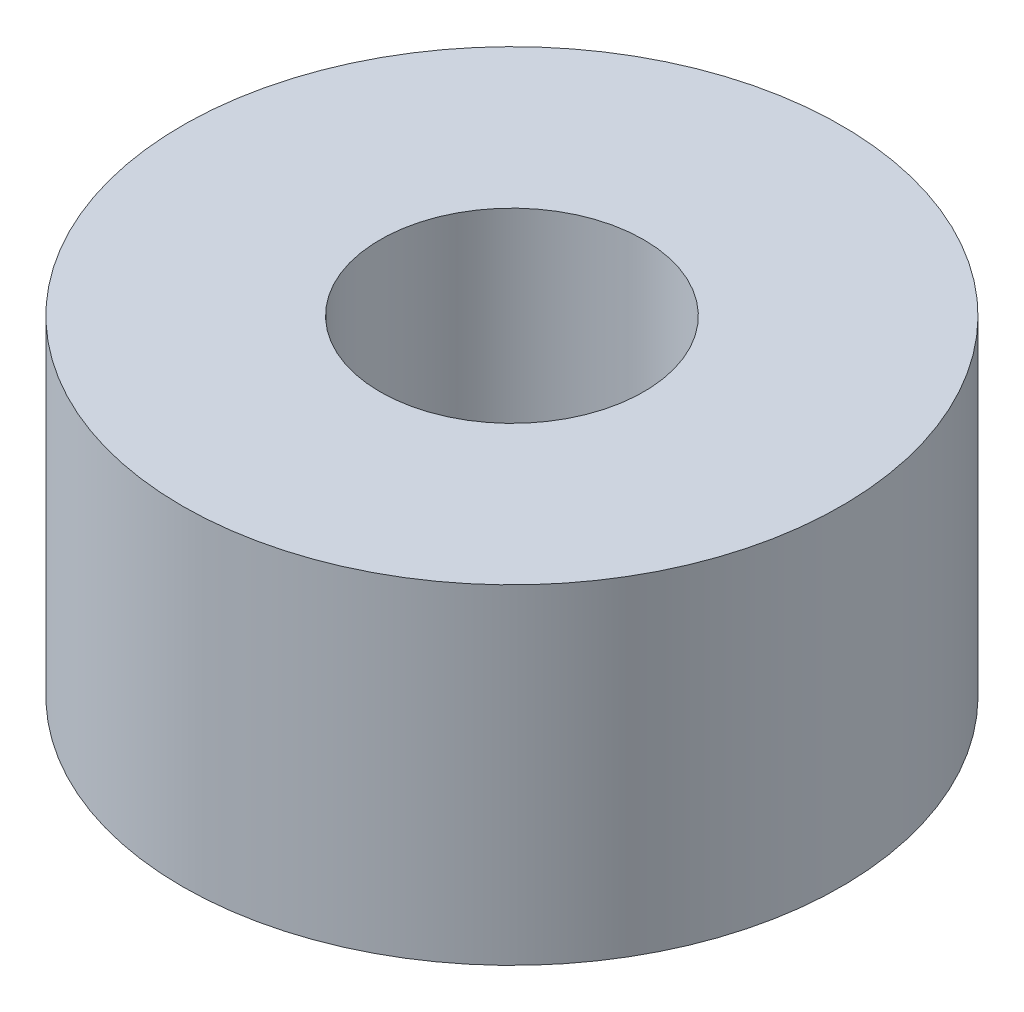
SolidWorks part; units mm, degrees
material "Chrome Stainless Steel"
ref_plane "Front Plane" through (0, 0, 0) normal (0, 0, 1) x (1, 0, 0)
ref_plane "Top Plane" through (0, 0, 0) normal (0, 1, 0) x (1, 0, 0)
ref_plane "Right Plane" through (0, 0, 0) normal (1, 0, 0) x (0, 0, -1)
sketch "Sketch2" plane through (0, 0, 0) normal (0, 1, 0) x (1, 0, 0)
  circle A0 centre (0, 0) radius 2.5
  circle A1 centre (0, 0) radius 1
  dimension "D1" = 5
  dimension "D2" = 2
extrude "Boss-Extrude1" add sketch "Sketch2" along normal blind 2.5
